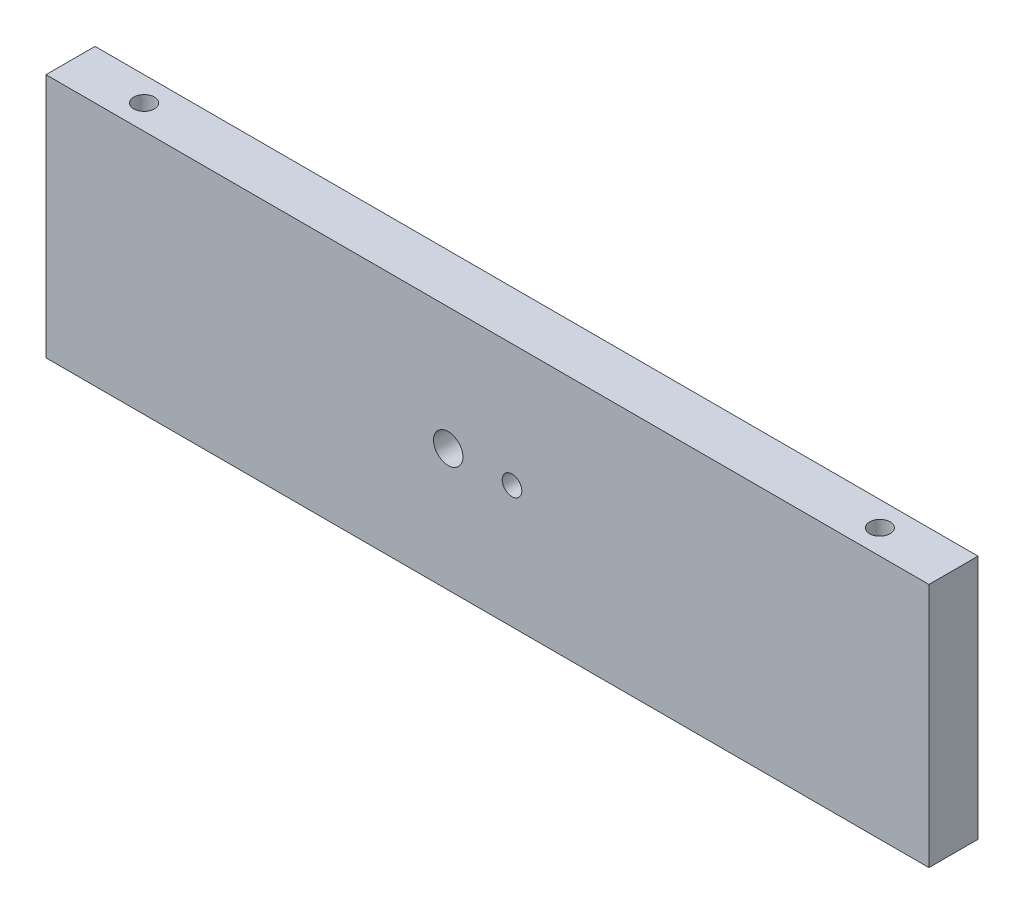
SolidWorks part; units mm, degrees
ref_plane "Front Plane" through (0, 0, 0) normal (0, 0, 1) x (1, 0, 0)
ref_plane "Top Plane" through (0, 0, 0) normal (0, 1, 0) x (1, 0, 0)
ref_plane "Right Plane" through (0, 0, 0) normal (1, 0, 0) x (0, 0, -1)
sketch "Sketch2" plane through (0, 0, 0) normal (0, 0, 1) x (1, 0, 0)
  line L1 (-90, -25) -> (90, -25)
  line L2 (-90, -25) -> (-90, 25)
  line L3 (-90, 25) -> (90, 25)
  line L4 (90, -25) -> (90, 25)
  line L5 (-90, -25) -> (90, 25) construction
  line L6 (-90, 25) -> (90, -25) construction
  point P0 (0, 0)
  dimension "D1" = 50
  dimension "D2" = 180
extrude "Boss-Extrude1" add sketch "Sketch2" along normal blind 10
sketch "Sketch3" plane through (0, 25, 0) normal (0, 1, 0) x (1, 0, 0)
  line L0 (90, 0) -> (-90, 0) construction
  line L1 (-90, -10) -> (-90, 0) construction
  line L2 (90, -10) -> (90, 0) construction
  point P0 (-75, -5)
  point P1 (75, -5)
  dimension "D1" = 5
  dimension "D2" = 5
  dimension "D3" = 15
  dimension "D4" = 15
sketch "Sketch6" plane through (0, 0, 10) normal (0, 0, 1) x (1, 0, 0)
  circle A0 centre (-8, 0) radius 3
  dimension "D1" = 6
  dimension "D2" = 8
extrude "Cut-Extrude1" cut sketch "Sketch6" against normal blind 10
hole_wizard "M5 Tapped Hole2" positions "Sketch8" profile "Sketch7" tap size "M5" standard "ISO"
sketch "Sketch8" plane through (0, 25, 0) normal (0, 1, 0) x (1, 0, 0)
  point P0 (-75, -5)
  point P3 (75, -5)
sketch "Sketch7" plane through (-75, 25, 5) normal (1, 0, 0) x (0, 0, 1)
  line L0 (0, 0) -> (0, 15.2618)
  line L1 (0, 15.2618) -> (2.1, 14)
  line L2 (2.1, 14) -> (2.1, 0)
  line L5 (2.1, 0) -> (0, 0)
  line L10 (0, 15.2618) -> (-2.1, 14) construction
  line L11 (0, -6.35) -> (0, 107.95) construction
  dimension "Tap Drill Dia." = 4.2
  dimension "Tap Drill Depth" = 14
  dimension "Drill Angle" = 118
cosmetic thread "Hole Thread3" parameters "D1"=10, "D2"=5
cosmetic thread "Hole Thread4" parameters "D1"=10, "D2"=5
sketch "Sketch9" plane through (0, 0, 10) normal (0, 0, 1) x (1, 0, 0)
  circle A0 centre (5, 0) radius 2
  circle A1 centre (-8, 0) radius 3 construction
  dimension "D1" = 4
  dimension "D2" = 13
extrude "Cut-Extrude2" cut sketch "Sketch9" against normal blind 10
